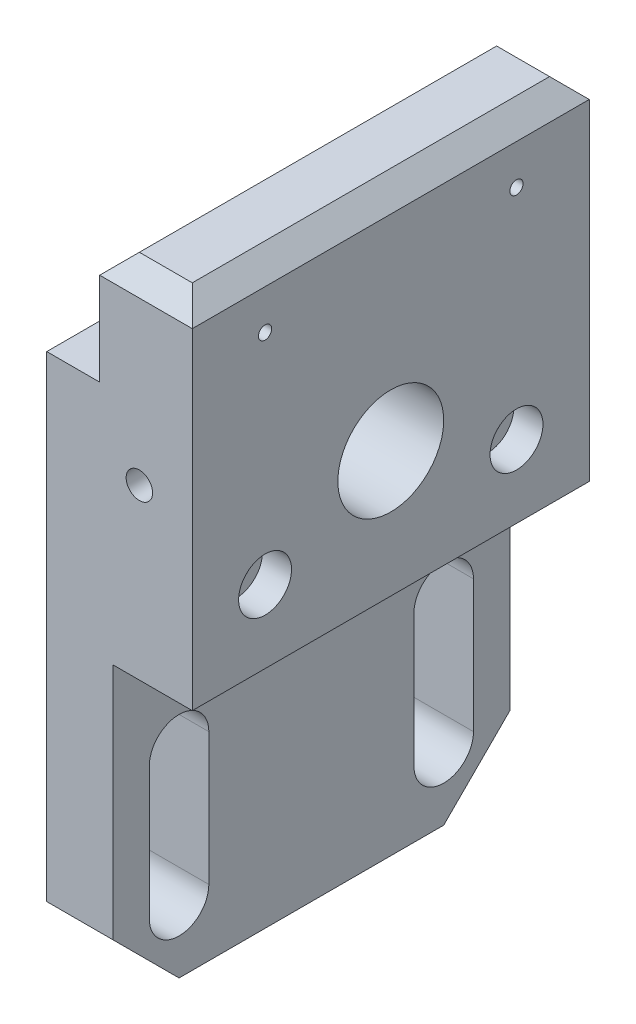
SolidWorks part; units mm, degrees
ref_plane "정면" through (0, 0, 0) normal (0, 0, 1) x (1, 0, 0)
ref_plane "윗면" through (0, 0, 0) normal (0, 1, 0) x (1, 0, 0)
ref_plane "우측면" through (0, 0, 0) normal (1, 0, 0) x (0, 0, -1)
sketch "스케치1" plane through (0, 0, 0) normal (0, 0, 1) x (1, 0, 0)
  line L0 (0, 0) -> (0, 82)
  line L1 (0, 82) -> (8, 82)
  line L2 (8, 82) -> (8, 99)
  line L3 (8, 99) -> (22, 99)
  line L4 (22, 99) -> (22, 46)
  line L5 (22, 46) -> (10, 46)
  line L6 (10, 46) -> (10, 0)
  line L7 (10, 0) -> (0, 0)
  point P7 (0, 0)
  dimension "D1" = 10
  dimension "D2" = 8
  dimension "D3" = 46
  dimension "D4" = 99
  dimension "D5" = 22
  dimension "D6" = 17
extrude "보스-돌출1" add sketch "스케치1" along normal mid plane 60
sketch "스케치2" plane through (0, 0, 0) normal (-1, 0, 0) x (0, 0, 1)
  line L0 (-20, 30) -> (-20, 10) construction
  line L1 (-15.5, 30) -> (-15.5, 10)
  line L2 (-24.5, 30) -> (-24.5, 10)
  line L3 (30, 0) -> (-30, 0) construction
  line L4 (0, 112.1064) -> (0, -30.5874) construction
  line L5 (20, 30) -> (20, 10) construction
  line L6 (15.5, 30) -> (15.5, 10)
  line L7 (24.5, 30) -> (24.5, 10)
  arc A0 (-15.5, 30) -> (-24.5, 30) centre (-20, 30) ccw
  arc A1 (-24.5, 10) -> (-15.5, 10) centre (-20, 10) ccw
  arc A2 (15.5, 30) -> (24.5, 30) centre (20, 30) cw
  arc A3 (24.5, 10) -> (15.5, 10) centre (20, 10) cw
  point P2 (-20, 20)
  point P14 (20, 20)
  dimension "D1" = 4.5
  dimension "D2" = 20
  dimension "D3" = 10
  dimension "D4" = 20
extrude "컷-돌출1" cut sketch "스케치2" against normal through all
hole_wizard "M4 소켓 머리 캡 나사용 카운터보어1" positions "스케치4" profile "스케치5" counterbore size "M4" standard "KS" end condition through all
sketch "스케치4" plane through (22, 0, 0) normal (1, 0, 0) x (0, 0, -1)
  line L0 (-30, 0) -> (30, 0) construction
  point P0 (-19, 57)
  point P2 (19, 57)
  point P3 (0, 0)
  point P5 (0, 0)
  dimension "D1" = 19
  dimension "D2" = 19
  dimension "D3" = 57
  dimension "D4" = 57
sketch "스케치5" plane through (22, 57, 19) normal (0, 1, 0) x (0, 0, -1)
  line L0 (0, 0) -> (0, 22)
  line L1 (0, 22) -> (2.25, 22)
  line L3 (2.25, 22) -> (2.25, 4.4)
  line L4 (2.25, 4.4) -> (4, 4.4)
  line L5 (4, 4.4) -> (4, 0)
  line L7 (4, 0) -> (0, 0)
  line L11 (0, -6.35) -> (0, 107.95) construction
  dimension "관통 구멍 지름" = 4.5
  dimension "관통 구멍 깊이" = 22
  dimension "카운터보어 지름" = 8
  dimension "카운터보어 깊이" = 4.4
sketch "스케치6" plane through (0, 0, 0) normal (-1, 0, 0) x (0, 0, 1)
  circle A0 centre (-19, 57) radius 5
  circle A1 centre (-19, 57) radius 2.25 construction
  circle A2 centre (19, 57) radius 5
  circle A3 centre (19, 57) radius 2.25 construction
  dimension "D1" = 10
  dimension "D2" = 10
extrude "컷-돌출2" cut sketch "스케치6" against normal blind 9
sketch "스케치7" plane through (22, 0, 0) normal (1, 0, 0) x (0, 0, -1)
  circle A0 centre (0, 65) radius 8
  point P2 (0, 0)
  dimension "D1" = 16
  dimension "D2" = 65
extrude "컷-돌출3" cut sketch "스케치7" against normal through all
hole_wizard "M4 여유 구멍1" positions "스케치8" profile "스케치9" hole size "M4" standard "KS" end condition through all
sketch "스케치8" plane through (22, 0, 0) normal (1, 0, 0) x (0, 0, -1)
  line L0 (-30, 99) -> (30, 99) construction
  point P0 (-19, 90)
  point P2 (19, 90)
  point P8 (19, 90)
  dimension "D1" = 19
  dimension "D2" = 19
  dimension "D3" = 9
sketch "스케치9" plane through (22, 90, 19) normal (0, 1, 0) x (0, 0, -1)
  line L0 (0, 0) -> (0, 22)
  line L1 (0, 22) -> (1, 22)
  line L2 (1, 22) -> (1, 0)
  line L5 (1, 0) -> (0, 0)
  line L11 (0, -6.35) -> (0, 107.95) construction
  dimension "관통 구멍 지름" = 2
  dimension "관통 구멍 깊이" = 22
hole_wizard "M4 여유 구멍2" positions "스케치10" profile "스케치11" hole size "M4" standard "KS" end condition through all
sketch "스케치10" plane through (0, 0, 30) normal (0, 0, 1) x (1, 0, 0)
  line L0 (0, 0) -> (10, 0) construction
  line L1 (22, 46) -> (22, 99) construction
  point P0 (14, 71.5)
  dimension "D1" = 71.5
  dimension "D2" = 8
sketch "스케치11" plane through (14, 71.5, 30) normal (1, 0, 0) x (0, -1, 0)
  line L0 (0, 0) -> (0, 60)
  line L1 (0, 60) -> (2, 60)
  line L2 (2, 60) -> (2, 0)
  line L5 (2, 0) -> (0, 0)
  line L11 (0, -6.35) -> (0, 107.95) construction
  dimension "관통 구멍 지름" = 4
  dimension "관통 구멍 깊이" = 60
chamfer "모따기1" distance 10 angle 45 2 edges at (5, 0, -30) (5, 0, 30)
chamfer "모따기2" distance 3 angle 45 4 edges at (22, 99, 0) (15, 99, 30) (8, 99, 0) (15, 99, -30)
